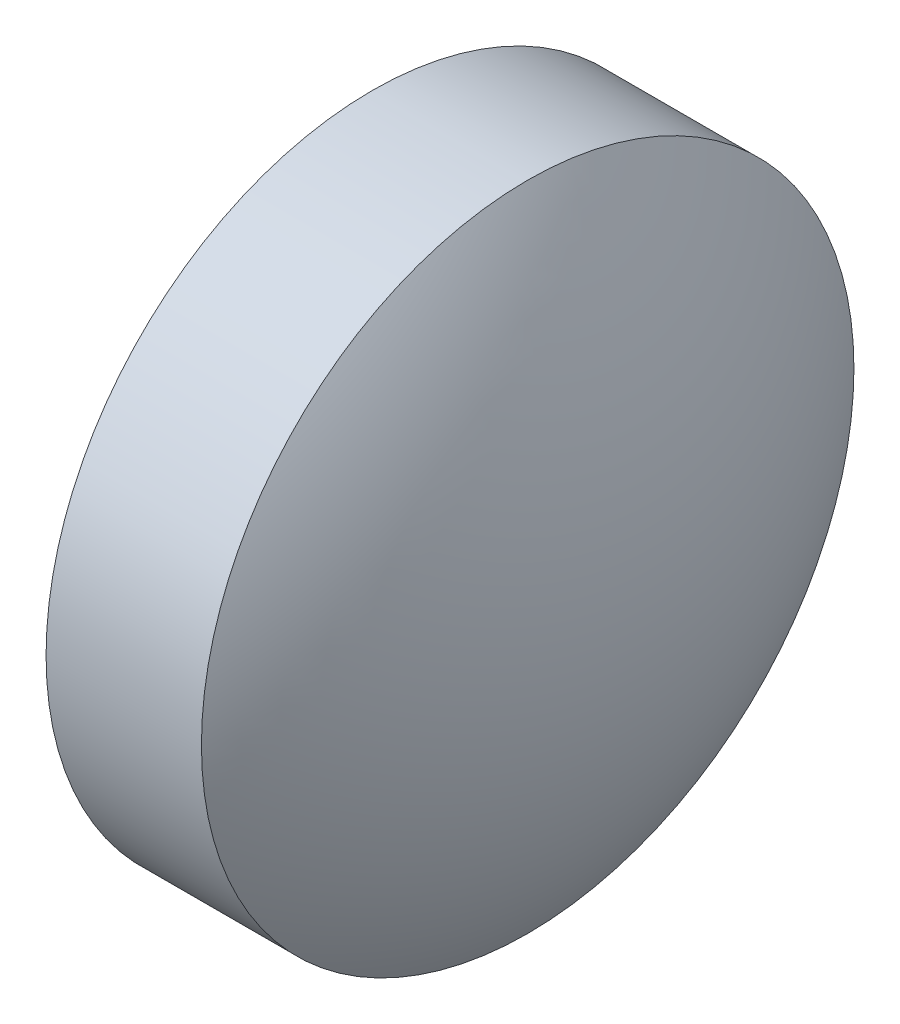
SolidWorks part; units mm, degrees
ref_plane "前视基准面" through (0, 0, 0) normal (0, 0, 1) x (1, 0, 0)
ref_plane "上视基准面" through (0, 0, 0) normal (0, 1, 0) x (1, 0, 0)
ref_plane "右视基准面" through (0, 0, 0) normal (1, 0, 0) x (0, 0, -1)
sketch "草图2" plane through (0, 0, 0) normal (0, 0, 1) x (1, 0, 0)
  line L0 (417.1492, -21.6774) -> (422.5442, -21.6774) construction
  line L1 (418.0098, -21.6774) -> (418.0098, -18.5274)
  line L2 (418.0098, -18.5274) -> (419.5098, -18.5274)
  line L3 (420.4498, -21.6774) -> (418.0098, -21.6774)
  arc A0 (420.4498, -21.6774) -> (419.5098, -18.5274) centre (414.7019, -21.6774) ccw
revolve "旋转2" add sketch "草图2" angle 360 about L0
